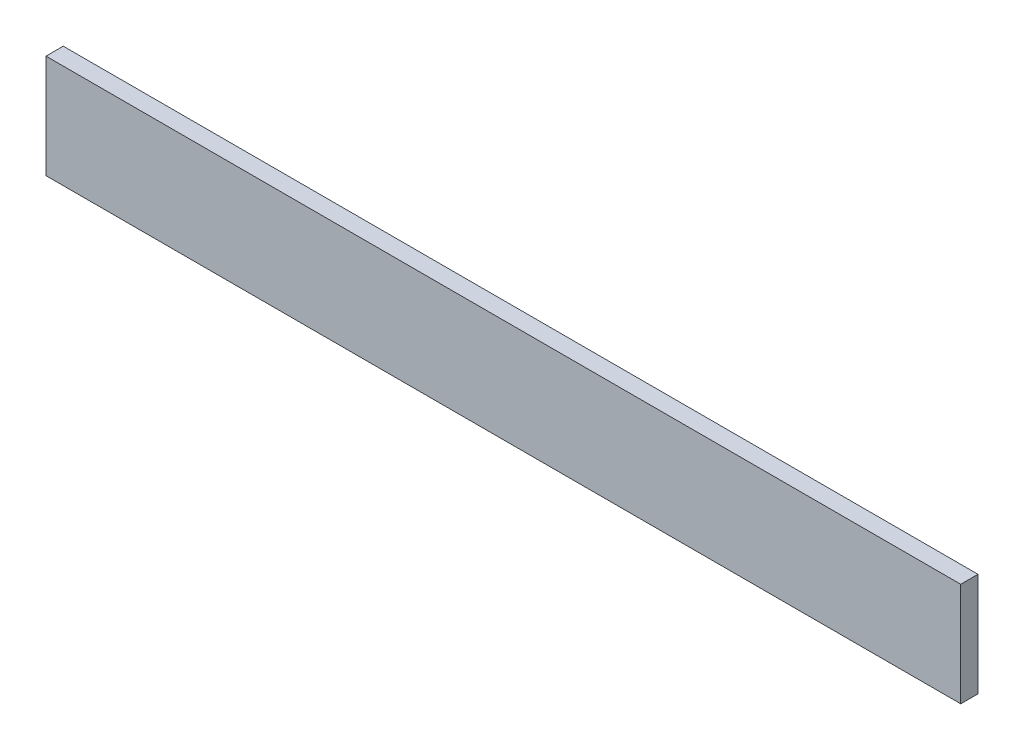
SolidWorks part; units mm, degrees
ref_plane "Front" through (0, 0, 0) normal (0, 0, 1) x (1, 0, 0)
ref_plane "Top" through (0, 0, 0) normal (0, 1, 0) x (1, 0, 0)
ref_plane "Right" through (0, 0, 0) normal (1, 0, 0) x (0, 0, -1)
sketch "Sketch1" plane through (0, 0, 0) normal (0, 0, 1) x (1, 0, 0)
  line L1 (0, 0) -> (265, 0)
  line L2 (0, 0) -> (0, 30)
  line L3 (0, 30) -> (265, 30)
  line L4 (265, 0) -> (265, 30)
  dimension "D1" = 265
  dimension "D2" = 30
extrude "Boss-Extrude1" add sketch "Sketch1" along normal blind 5
